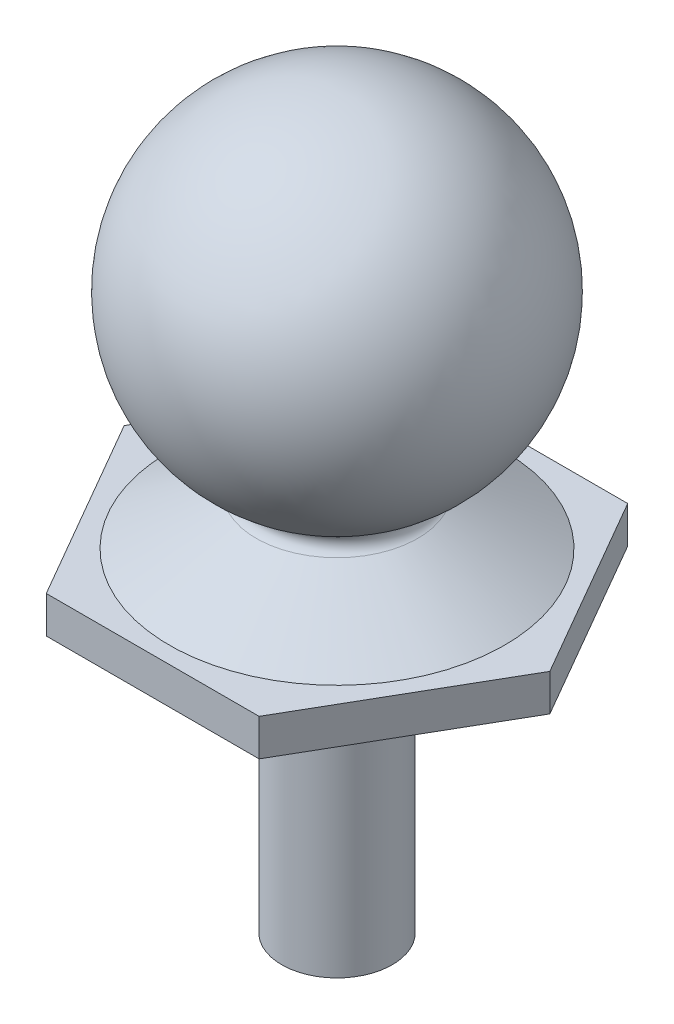
SolidWorks part; units mm, degrees
ref_plane "Front Plane" through (0, 0, 0) normal (0, 0, 1) x (1, 0, 0)
ref_plane "Top Plane" through (0, 0, 0) normal (0, 1, 0) x (1, 0, 0)
ref_plane "Right Plane" through (0, 0, 0) normal (1, 0, 0) x (0, 0, -1)
sketch "Sketch1" plane through (0, 0, 0) normal (0, 0, 1) x (1, 0, 0)
  line L4 (0, -6.2096) -> (5, -6.2096) construction
  line L8 (2.1921, -4.7053) -> (4.85, -6.2096)
  line L9 (4.85, -6.2096) -> (5, -6.2096)
  line L10 (5, -6.2096) -> (5, -7.0378)
  line L14 (1.5, -7.0378) -> (1.5, -15.0679)
  line L17 (1.5, -7.0378) -> (5, -7.0378)
  line L18 (0, 4.7096) -> (0, -15.0679)
  line L19 (0, -15.0679) -> (1.5, -15.0679)
  arc A0 (2.2039, -4.1622) -> (0, 4.7096) centre (0, 0) ccw
  arc A2 (2.2039, -4.1622) -> (2.1921, -4.7053) centre (2.344, -4.4369) ccw
  point P6 (2.0356, -4.4302)
  dimension "D3" = 0.8282
  dimension "D6" = 4.7096
  dimension "D7" = 0.3084
  dimension "D2" = 1.5
  dimension "D4" = 4.85
  dimension "D5" = 8.0301
  dimension "D8" = 5
  dimension "D9" = 11.7475
  dimension "D10" = 2.6009
  dimension "D11" = 2.0356
revolve "Revolve1" add sketch "Sketch1" angle 360 about L18
sketch "Sketch3" plane through (0, -7.0378, 0) normal (0, -1, 0) x (1, 0, 0)
  line L1 (5.7735, 0) -> (2.8868, 5)
  line L2 (2.8868, 5) -> (-2.8868, 5)
  line L3 (-2.8868, 5) -> (-5.7735, 0)
  line L4 (-5.7735, 0) -> (-2.8868, -5)
  line L5 (-2.8868, -5) -> (2.8868, -5)
  line L6 (2.8868, -5) -> (5.7735, 0)
  circle A0 centre (0, 0) radius 5 construction
  point P1 (0, 0)
  dimension "D1" = 10
extrude "Boss-Extrude1" add sketch "Sketch3" against normal blind 1
